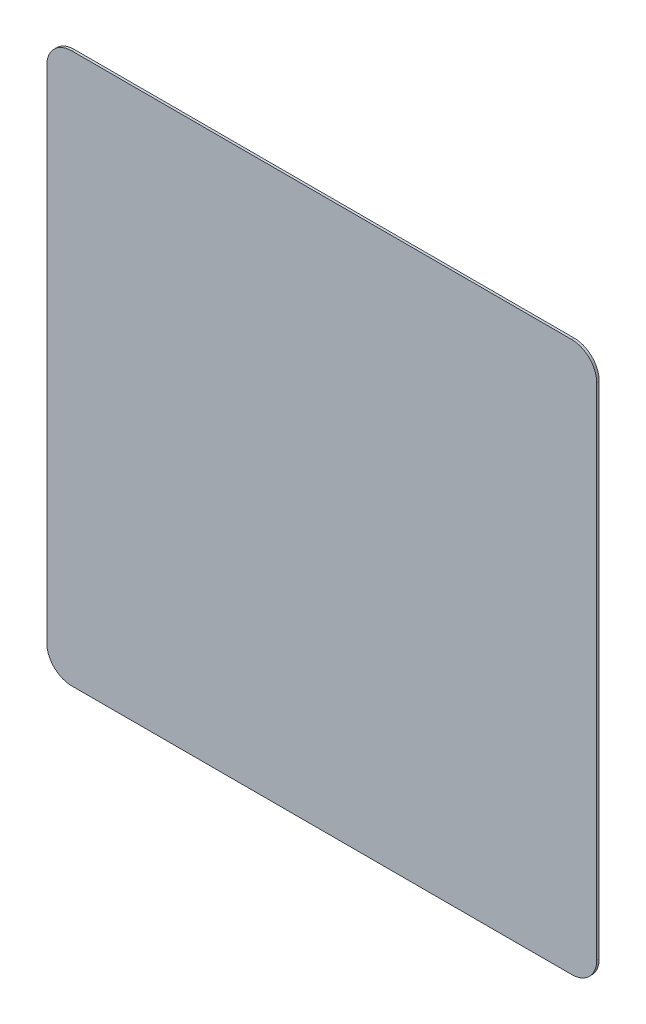
SolidWorks part; units mm, degrees
ref_plane "Front Plane" through (0, 0, 0) normal (0, 0, 1) x (1, 0, 0)
ref_plane "Top Plane" through (0, 0, 0) normal (0, 1, 0) x (1, 0, 0)
ref_plane "Right Plane" through (0, 0, 0) normal (1, 0, 0) x (0, 0, -1)
sketch "Sketch1" plane through (0, 0, 0) normal (0, 0, 1) x (1, 0, 0)
  line L0 (-2.75, -2.75) -> (-2.75, 2.75)
  line L1 (-2.5, -2.5) -> (2.5, -2.5)
  line L2 (-2.5, -2.5) -> (-2.5, 2.5)
  line L3 (-2.5, 2.5) -> (2.5, 2.5)
  line L4 (2.5, -2.5) -> (2.5, 2.5)
  line L5 (-2.5, -2.5) -> (2.5, 2.5) construction
  line L6 (-2.5, 2.5) -> (2.5, -2.5) construction
  line L11 (-2.75, 2.75) -> (2.75, 2.75)
  line L12 (2.75, -2.75) -> (2.75, 2.75)
  line L13 (-2.75, -2.75) -> (2.75, -2.75)
  point P0 (0, 0)
  dimension "D1" = 5
  dimension "D4" = 0.25
extrude "Boss-Extrude1" add sketch "Sketch1" along normal blind 0.025
fillet "Fillet1" radius 0.25 4 edges at (2.75, -2.75, 0.0125) (2.75, 2.75, 0.0125) (-2.75, 2.75, 0.0125) (-2.75, -2.75, 0.0125)
